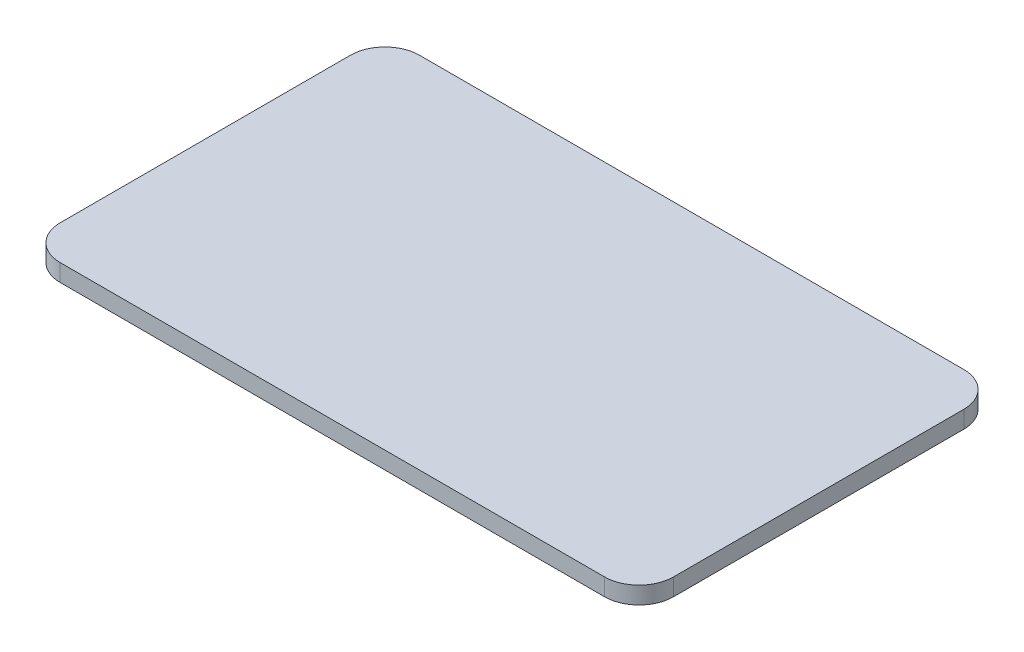
SolidWorks part; units mm, degrees
ref_plane "Front" through (0, 0, 0) normal (0, 0, 1) x (1, 0, 0)
ref_plane "Top" through (0, 0, 0) normal (0, 1, 0) x (1, 0, 0)
ref_plane "Right" through (0, 0, 0) normal (1, 0, 0) x (0, 0, -1)
sketch "Sketch1" plane through (0, 0, 0) normal (0, 1, 0) x (1, 0, 0)
  line L1 (-39.45, -26.035) -> (39.45, -26.035)
  line L2 (-44.45, -21.035) -> (-44.45, 21.035)
  line L3 (-39.45, 26.035) -> (39.45, 26.035)
  line L4 (44.45, -21.035) -> (44.45, 21.035)
  line L5 (-44.45, -26.035) -> (44.45, 26.035) construction
  line L6 (-44.45, 26.035) -> (44.45, -26.035) construction
  arc A0 (39.45, -26.035) -> (44.45, -21.035) centre (39.45, -21.035) ccw
  arc A1 (-39.45, -26.035) -> (-44.45, -21.035) centre (-39.45, -21.035) cw
  arc A2 (-44.45, 21.035) -> (-39.45, 26.035) centre (-39.45, 21.035) cw
  arc A3 (39.45, 26.035) -> (44.45, 21.035) centre (39.45, 21.035) cw
  point P0 (0, 0)
  dimension "D3" = 5
  dimension "D1" = 88.9
  dimension "D2" = 52.07
extrude "Boss-Extrude1" add sketch "Sketch1" along normal blind 2.5
